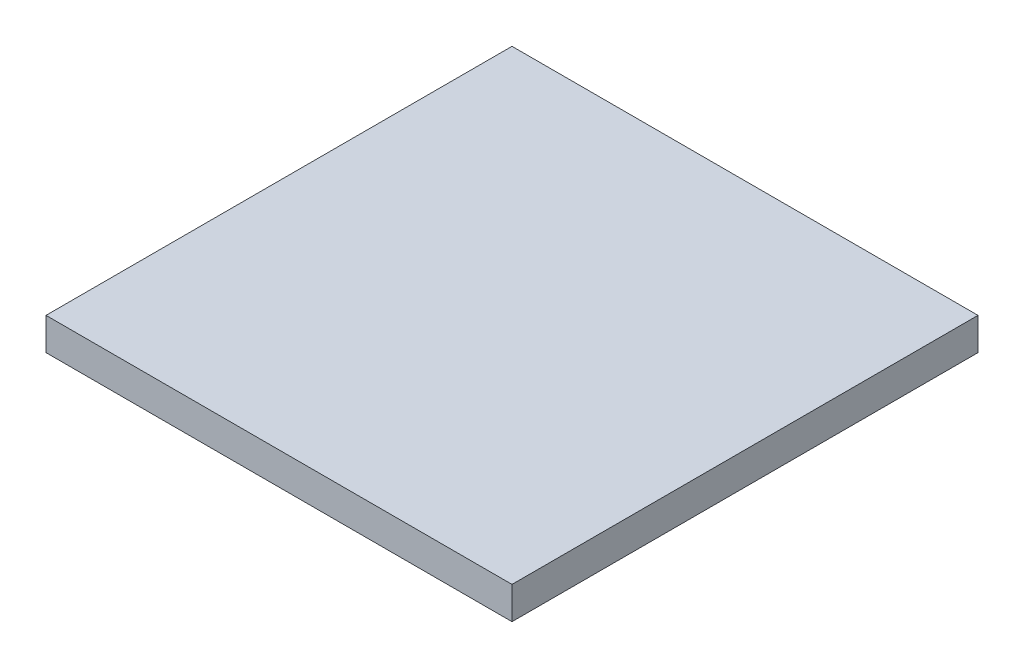
SolidWorks part; units mm, degrees
ref_plane "前视基准面" through (0, 0, 0) normal (0, 0, 1) x (1, 0, 0)
ref_plane "上视基准面" through (0, 0, 0) normal (0, 1, 0) x (1, 0, 0)
ref_plane "右视基准面" through (0, 0, 0) normal (1, 0, 0) x (0, 0, -1)
other "Configuration Table"
sketch "草图1" plane through (0, 0, 0) normal (0, 1, 0) x (1, 0, 0)
  line L1 (-15, -15) -> (15, -15)
  line L2 (-15, -15) -> (-15, 15)
  line L3 (-15, 15) -> (15, 15)
  line L4 (15, -15) -> (15, 15)
  line L5 (-15, -15) -> (15, 15) construction
  line L6 (-15, 15) -> (15, -15) construction
  point P0 (0, 0)
  dimension "D1" = 30
  dimension "D2" = 30
extrude "凸台-拉伸1" add sketch "草图1" along normal blind 2.08
